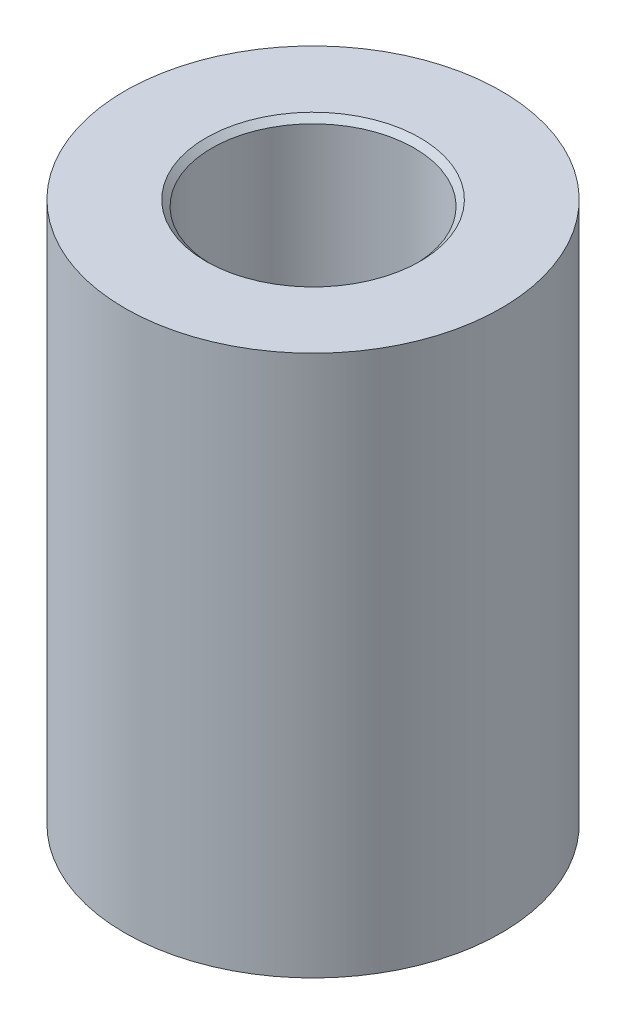
SolidWorks part; units mm, degrees
ref_plane "Front Plane" through (0, 0, 0) normal (0, 0, 1) x (1, 0, 0)
ref_plane "Top Plane" through (0, 0, 0) normal (0, 1, 0) x (1, 0, 0)
ref_plane "Right Plane" through (0, 0, 0) normal (1, 0, 0) x (0, 0, -1)
sketch "Sketch1" plane through (0, 0, 0) normal (0, 1, 0) x (1, 0, 0)
  circle A0 centre (0, 0) radius 4
  dimension "D1" = 8
extrude "Boss-Extrude1" add sketch "Sketch1" along normal mid plane 11.5
sketch "Sketch4" plane through (0, 5.75, 0) normal (0, 1, 0) x (1, 0, 0)
  point P0 (0, 0)
hole_wizard "M4 Clearance Hole1" positions "Sketch4" profile "Sketch5" hole size "M4" standard "ANSI Metric" end condition through all
sketch "Sketch5" plane through (0, 5.75, 0) normal (1, 0, 0) x (0, 0, 1)
  line L0 (0, 0) -> (0, 11.5)
  line L1 (0, 11.5) -> (2.15, 11.5)
  line L2 (2.15, 11.5) -> (2.15, 0.125)
  line L3 (2.15, 0.125) -> (2.275, 0)
  line L5 (2.275, 0) -> (0, 0)
  line L6 (-2.15, 0.125) -> (-2.275, 0) construction
  line L11 (0, -6.35) -> (0, 107.95) construction
  dimension "Thru Hole Dia." = 4.3
  dimension "Thru Hole Depth" = 11.5
  dimension "Near C'Sink Dia." = 4.55
  dimension "Near C'Sink Angle" = 90
